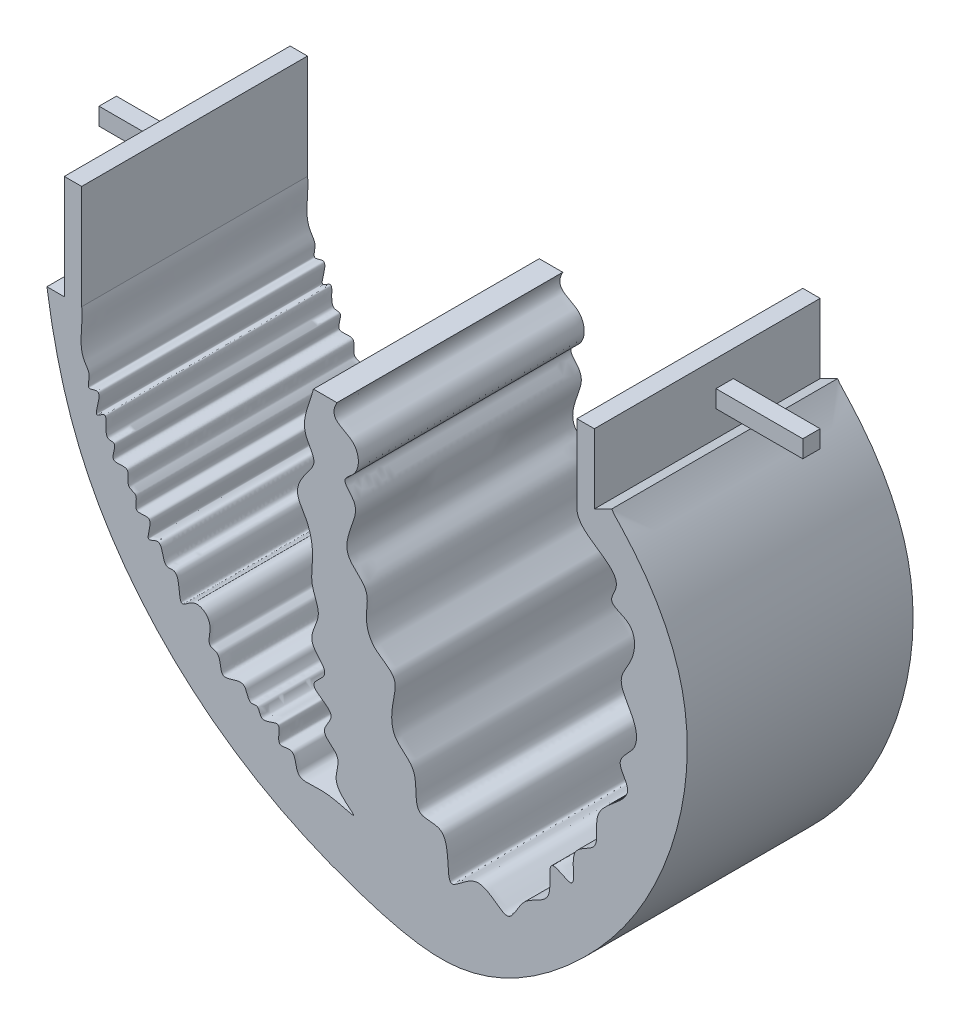
SolidWorks part; units mm, degrees
ref_plane "Front Plane" through (0, 0, 0) normal (0, 0, 1) x (1, 0, 0)
ref_plane "Top Plane" through (0, 0, 0) normal (0, 1, 0) x (1, 0, 0)
ref_plane "Right Plane" through (0, 0, 0) normal (1, 0, 0) x (0, 0, -1)
sketch "Sketch1" plane through (0, 0, 0) normal (0, 0, 1) x (1, 0, 0)
  line L0 (155.9186, 311.1659) -> (244.8186, 311.1659) construction
  line L1 (155.9893, 303.5522) -> (158.5293, 303.5522)
  line L2 (194.9578, 310.0742) -> (198.3939, 310.0742)
  line L3 (236.0285, 315.4292) -> (238.5685, 316.6992)
  line L4 (158.5293, 303.5522) -> (158.5293, 318.7922)
  line L5 (158.5293, 318.7922) -> (161.0693, 318.7922)
  line L6 (161.0693, 318.7922) -> (161.0693, 303.5522)
  line L7 (233.4885, 314.1592) -> (233.4885, 325.5892)
  line L8 (233.4885, 325.5892) -> (236.0285, 325.5892)
  line L9 (236.0285, 325.5892) -> (236.0285, 315.4292)
  spline S0 degree 3 poles (155.9893, 303.5522) (156.9874, 296.7118) (160.9033, 280.7584) (177.6798, 260.2526) (198.0088, 250.0527) (218.1215, 245.4575) (234.4341, 256.0632) (247.821, 274.206) (252.0255, 297.8643) (243.4922, 311.504) (238.9441, 316.1409) (238.5685, 316.6992) knots 0.120047 0.120047 0.120047 0.120047 0.184834 0.273022 0.359649 0.397817 0.461195 0.526427 0.612455 0.666069 0.672634 0.672634 0.672634 0.672634
  spline S8 degree 3 poles (161.0693, 303.5522) (161.4107, 301.5133) (160.1814, 297.9994) (162.5192, 295.5777) (161.6056, 293.2687) (164.6643, 294.9317) (162.279, 289.8336) (165.3239, 292.6173) (163.9822, 288.4957) (166.4928, 288.8819) (164.6675, 285.6617) (168.6137, 287.0817) (167.3459, 284.0469) (169.5425, 283.8413) (168.2939, 281.067) (172.1277, 282.5033) (169.9448, 278.1295) (173.1697, 280.3318) (172.7201, 276.4467) (175.7412, 277.3937) (174.8347, 271.7803) (177.7194, 275.1309) (180.6936, 272.9506) (179.1306, 269.9321) (181.5949, 269.7054) (180.8903, 265.7406) (185.2155, 268.8503) (185.3098, 265.4382) (187.0121, 266.0623) (187.1786, 263.6209) (190.7598, 266.317) (189.2184, 261.8895) (192.3846, 263.3381) (192.2241, 259.0148) (196.3795, 260.5619) (202.9745, 257.9478) (197.0023, 261.6686) (199.6703, 265.4188) (195.335, 267.3237) (199.1432, 270.5694) (193.2707, 272.3433) (198.083, 274.9882) (193.2964, 277.883) (196.5776, 281.6333) (194.3901, 285.0063) (195.0388, 288.8547) (194.5242, 292.56) (191.9703, 295.8002) (193.5815, 298.5951) (195.7144, 301.0169) (192.4266, 304.655) (194.526, 308.0675) (194.9578, 310.0742) knots 0 0 0 0 0.051397 0.063492 0.07499 0.084165 0.106718 0.115019 0.13647 0.141731 0.157651 0.17253 0.188747 0.195795 0.210241 0.223932 0.2433 0.253185 0.275038 0.28133 0.309962 0.32445 0.345973 0.366482 0.372547 0.392341 0.415465 0.430589 0.436356 0.446399 0.464594 0.482023 0.494083 0.511854 0.542178 0.575014 0.602691 0.629484 0.651572 0.671253 0.699149 0.718062 0.745129 0.77589 0.801425 0.826133 0.86225 0.884781 0.910268 0.92777 0.949733 1 1 1 1
  spline S9 degree 3 poles (198.3939, 310.0742) (196.9154, 307.349) (201.6031, 307.5181) (201.8349, 302.5162) (198.7399, 300.8409) (201.6659, 298.6817) (200.4848, 295.3887) (198.9993, 291.2414) (203.419, 288.86) (202.3635, 284.9727) (203.4626, 281.4078) (207.5743, 279.8285) (206.2925, 275.6436) (206.311, 271.5042) (210.8333, 269.3982) (209.0763, 263.2826) (215.6152, 264.5807) (213.5483, 254.5147) (219.2555, 261.805) (223.5966, 255.4758) (225.4091, 261.6818) (230.5567, 261.889) (228.6645, 268.7824) (234.0272, 264.7747) (231.7903, 271.3599) (237.3043, 272.1367) (234.9856, 278.5392) (242.8762, 281.0009) (238.738, 285.5395) (242.4252, 287.7196) (242.1688, 291.9541) (238.84, 295.4724) (242.0193, 299.1085) (242.264, 303.7591) (237.7623, 304.5891) (241.38, 309.7317) (233.6241, 310.9404) (233.4885, 314.1592) knots 0 0 0 0 0.037555 0.064866 0.078213 0.095177 0.117489 0.147696 0.176756 0.200025 0.224822 0.251288 0.27607 0.305558 0.331912 0.368046 0.38825 0.432206 0.462647 0.497673 0.524432 0.557499 0.585086 0.604403 0.633249 0.659677 0.689393 0.740628 0.760008 0.784769 0.807611 0.843275 0.868456 0.900646 0.920575 0.934057 1 1 1 1
  dimension "D1" = 88.9
  dimension "D2" = 15.24
  dimension "D3" = 10.16
  dimension "D4" = 11.43
  dimension "D5" = 2.54
  dimension "D6" = 2.54
extrude "Boss-Extrude1" add sketch "Sketch1" along normal blind 33.02
sketch "Sketch2" plane through (158.5293, 0, 0) normal (-1, 0, 0) x (0, 0, 1)
  line L0 (33.02, 318.7922) -> (33.02, 303.5522) construction
  line L1 (12.7, 312.4422) -> (15.24, 312.4422)
  line L2 (12.7, 312.4422) -> (12.7, 309.9022)
  line L3 (12.7, 309.9022) -> (15.24, 309.9022)
  line L4 (15.24, 312.4422) -> (15.24, 309.9022)
  line L5 (12.7, 312.4422) -> (15.24, 309.9022) construction
  line L6 (12.7, 309.9022) -> (15.24, 312.4422) construction
  line L8 (33.02, 318.7922) -> (0, 318.7922) construction
  point P0 (13.97, 311.1722)
  dimension "D1" = 2.54
  dimension "D2" = 2.54
  dimension "D3" = 19.05
  dimension "D4" = 7.62
sketch "Sketch3" plane through (236.0285, 0, 0) normal (1, 0, 0) x (0, 0, -1)
  line L1 (-15.24, 321.7792) -> (-12.7, 321.7792)
  line L2 (-15.24, 321.7792) -> (-15.24, 319.2392)
  line L3 (-15.24, 319.2392) -> (-12.7, 319.2392)
  line L4 (-12.7, 321.7792) -> (-12.7, 319.2392)
  line L5 (-15.24, 321.7792) -> (-12.7, 319.2392) construction
  line L6 (-15.24, 319.2392) -> (-12.7, 321.7792) construction
  line L7 (-33.02, 315.4292) -> (-33.02, 325.5892) construction
  line L8 (-33.02, 325.5892) -> (0, 325.5892) construction
  point P0 (-13.97, 320.5092)
  dimension "D1" = 19.05
  dimension "D2" = 2.54
  dimension "D3" = 2.54
  dimension "D4" = 5.08
extrude "Boss-Extrude2" add sketch "Sketch2" along normal blind 12.7
extrude "Boss-Extrude3" add sketch "Sketch3" along normal blind 12.7
